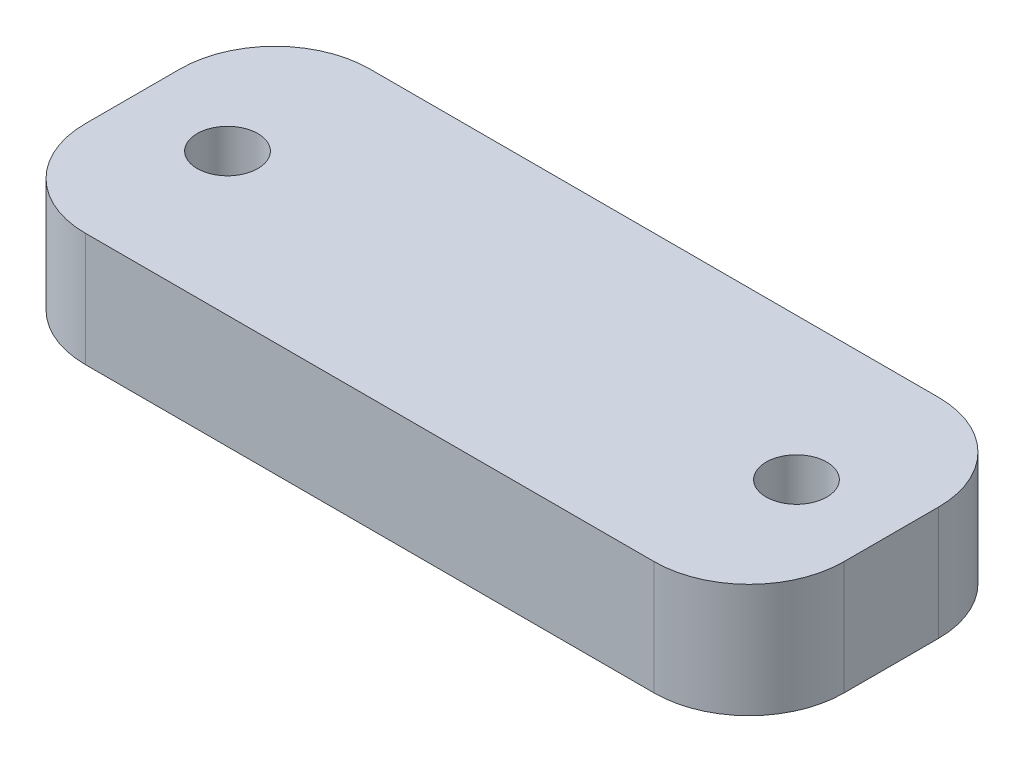
SolidWorks part; units mm, degrees
material "Maple"
ref_plane "Front Plane" through (0, 0, 0) normal (0, 0, 1) x (1, 0, 0)
ref_plane "Top Plane" through (0, 0, 0) normal (0, 1, 0) x (1, 0, 0)
ref_plane "Right Plane" through (0, 0, 0) normal (1, 0, 0) x (0, 0, -1)
sketch "Sketch1" plane through (0, 0, 0) normal (0, 1, 0) x (1, 0, 0)
  line L1 (-20, 7.5) -> (20, 7.5)
  line L2 (-20, 7.5) -> (-20, -7.5)
  line L3 (-20, -7.5) -> (20, -7.5)
  line L4 (20, 7.5) -> (20, -7.5)
  line L5 (-20, 7.5) -> (20, -7.5) construction
  line L6 (-20, -7.5) -> (20, 7.5) construction
  point P0 (0, 0)
  dimension "D1" = 40
  dimension "D2" = 15
extrude "Boss-Extrude1" add sketch "Sketch1" along normal blind 6
ref_plane "Plane1" through (0, 3, 0) normal (0, 1, 0) x (1, 0, 0)
hole_wizard "M3 Clearance Hole1" positions "Sketch3" profile "Sketch2" hole size "M3" standard "ANSI Metric" end condition through all
sketch "Sketch3" plane through (0, 6, 0) normal (0, 1, 0) x (1, 0, 0)
  line L0 (-15, 0) -> (15, 0) construction
  point P0 (-15, 0)
  point P2 (15, 0)
  dimension "D1" = 30
sketch "Sketch2" plane through (-15, 6, 0) normal (1, 0, 0) x (0, 0, 1)
  line L0 (0, 0) -> (0, 6)
  line L1 (0, 6) -> (1.6, 6)
  line L2 (1.6, 6) -> (1.6, 0)
  line L5 (1.6, 0) -> (0, 0)
  line L11 (0, -6.35) -> (0, 107.95) construction
  dimension "Thru Hole Dia." = 3.2
  dimension "Thru Hole Depth" = 6
fillet "Fillet1" radius 5 4 edges at (20, 3, 7.5) (-20, 3, -7.5) (20, 3, -7.5) (-20, 3, 7.5)
